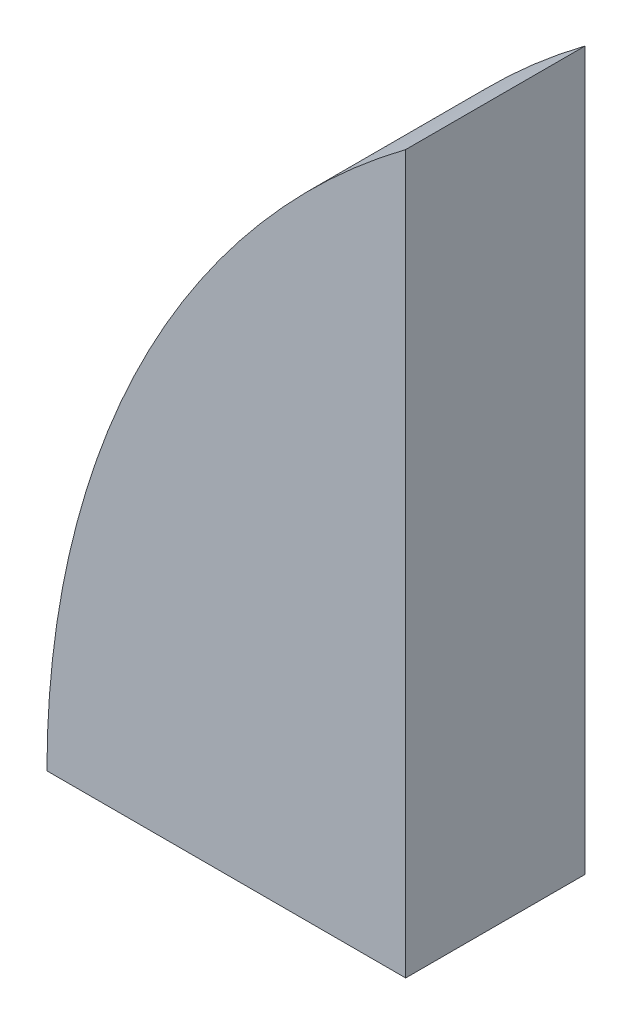
SolidWorks part; units mm, degrees
ref_plane "Front Plane" through (0, 0, 0) normal (0, 0, 1) x (1, 0, 0)
ref_plane "Top Plane" through (0, 0, 0) normal (0, 1, 0) x (1, 0, 0)
ref_plane "Right Plane" through (0, 0, 0) normal (1, 0, 0) x (0, 0, -1)
sketch "Sketch1" plane through (0, 0, 0) normal (0, 0, 1) x (1, 0, 0)
  line L0 (6.35, 12.7) -> (12.7, 12.7)
  line L1 (0, 0) -> (12.7, 0)
  line L2 (0, 0) -> (0, 38.1)
  line L3 (0, 38.1) -> (12.7, 38.1)
  line L4 (12.7, 0) -> (12.7, 38.1)
  line L5 (0, 12.7) -> (6.35, 12.7)
  line L6 (0, 12.7) -> (0, 0)
  line L7 (0, 0) -> (6.35, 0)
  line L8 (6.35, 12.7) -> (6.35, 0)
  arc A0 (0, 12.7) -> (12.7, 38.1) centre (31.75, 12.7) cw
  dimension "D1" = 6.35
  dimension "D2" = 12.7
  dimension "D3" = 12.7
  dimension "D4" = 38.1
extrude "Boss-Extrude1" add sketch "Sketch1" along normal blind 6.35 contours A0 L5 L8 L1 L4
